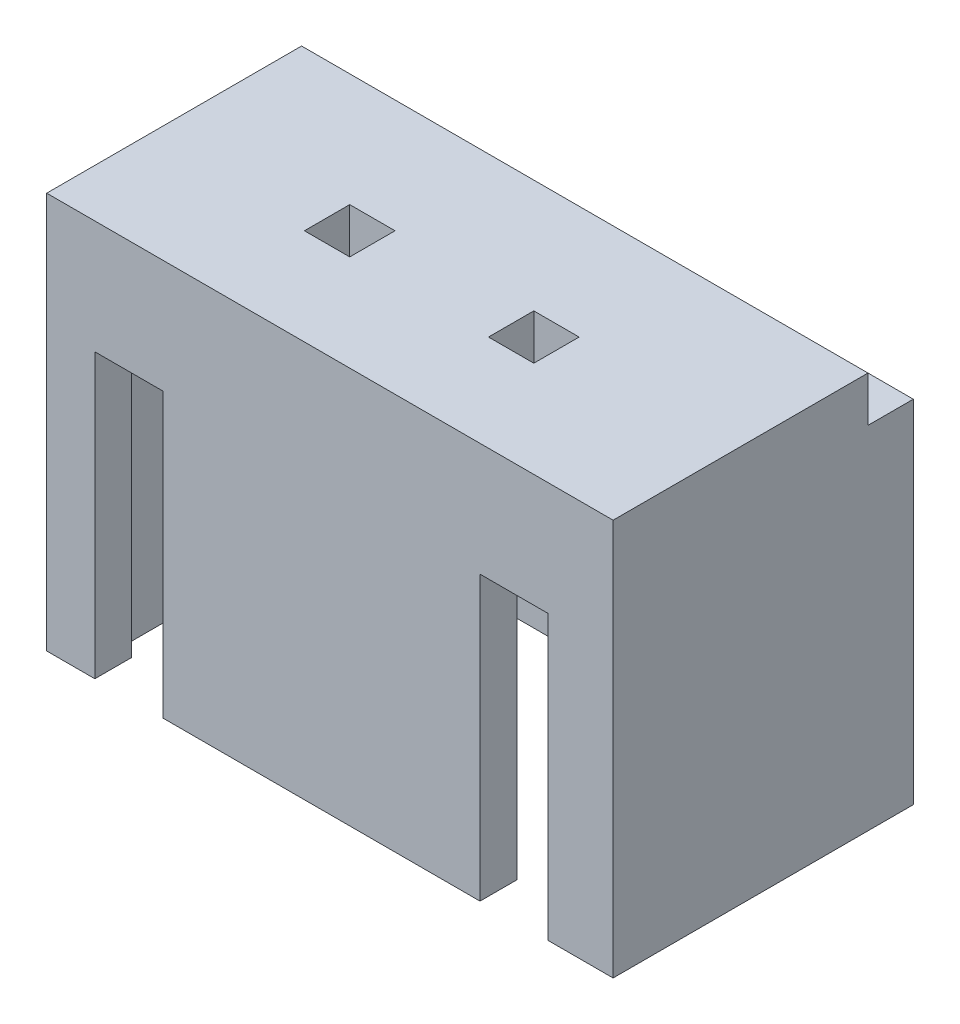
SolidWorks part; units mm, degrees
ref_plane "Front Plane" through (0, 0, 0) normal (0, 0, 1) x (1, 0, 0)
ref_plane "Top Plane" through (0, 0, 0) normal (0, 1, 0) x (1, 0, 0)
ref_plane "Right Plane" through (0, 0, 0) normal (1, 0, 0) x (0, 0, -1)
sketch "Sketch1" plane through (0, 0, 0) normal (0, 1, 0) x (1, 0, 0)
  line L1 (-5, -2.65) -> (5, -2.65)
  line L2 (-5, -2.65) -> (-5, 2.65)
  line L3 (-5, 2.65) -> (5, 2.65)
  line L4 (5, -2.65) -> (5, 2.65)
  line L5 (-5, -2.65) -> (5, 2.65) construction
  line L6 (-5, 2.65) -> (5, -2.65) construction
  point P0 (0, 0)
  dimension "D1" = 10
  dimension "D2" = 5.3
extrude "Boss-Extrude1" add sketch "Sketch1" along normal blind 7
sketch "Sketch3" plane through (0, 0, 0) normal (0, -1, 0) x (1, 0, 0)
  line L1 (-4.4, -2) -> (4.4, -2)
  line L2 (-4.4, -2) -> (-4.4, 2)
  line L3 (-4.4, 2) -> (4.4, 2)
  line L4 (4.4, -2) -> (4.4, 2)
  line L5 (-4.4, -2) -> (4.4, 2) construction
  line L6 (-4.4, 2) -> (4.4, -2) construction
  point P0 (0, 0)
  dimension "D1" = 8.8
  dimension "D2" = 4
extrude "Cut-Extrude1" cut sketch "Sketch3" against normal blind 5
sketch "Sketch4" plane through (0, 0, 2.65) normal (0, 0, 1) x (1, 0, 0)
  line L0 (-5, 0) -> (5, 0) construction
  line L1 (-4.15, 0) -> (-2.95, 0)
  line L2 (-4.15, 0) -> (-4.15, 5)
  line L3 (-4.15, 5) -> (-2.95, 5)
  line L4 (-2.95, 0) -> (-2.95, 5)
  line L6 (2.65, 0) -> (3.85, 0)
  line L7 (2.65, 0) -> (2.65, 5)
  line L8 (2.65, 5) -> (3.85, 5)
  line L9 (3.85, 0) -> (3.85, 5)
  dimension "D1" = 1.2
  dimension "D2" = 1.2
  dimension "D3" = 4.15
  dimension "D4" = 8
  dimension "D5" = 5
extrude "Cut-Extrude2" cut sketch "Sketch4" against normal blind 4
sketch "Sketch5" plane through (0, 7, 0) normal (0, 1, 0) x (1, 0, 0)
  line L0 (5, -2.65) -> (5, 2.65) construction
  line L1 (5, 1.85) -> (-5, 1.85)
  line L2 (5, 1.85) -> (5, 2.65)
  line L3 (5, 2.65) -> (-5, 2.65)
  line L4 (-5, 1.85) -> (-5, 2.65)
  dimension "D1" = 0.8
extrude "Cut-Extrude3" cut sketch "Sketch5" against normal blind 0.8 contours L1 L4 L3 L2
sketch "Sketch6" plane through (0, 7, 0) normal (0, 1, 0) x (1, 0, 0)
  line L2 (1.9, -0.15) -> (1.1, -0.15)
  line L3 (1.9, -0.15) -> (1.9, -0.95)
  line L4 (1.9, -0.95) -> (1.1, -0.95)
  line L5 (1.1, -0.15) -> (1.1, -0.95)
  line L6 (-1.35, -0.95) -> (-2.15, -0.95)
  line L7 (-1.35, -0.95) -> (-1.35, -0.15)
  line L8 (-1.35, -0.15) -> (-2.15, -0.15)
  line L9 (-2.15, -0.95) -> (-2.15, -0.15)
extrude "Cut-Extrude4" cut sketch "Sketch6" against normal blind 10
sketch "Sketch7" plane through (0, 5, 0) normal (0, -1, 0) x (1, 0, 0)
  line L0 (4.4, -2) -> (4.4, 2) construction
  line L1 (-4.4, -2) -> (4.4, -2)
  line L2 (-4.4, -2) -> (-4.4, -1)
  line L3 (-4.4, -1) -> (4.4, -1)
  line L4 (4.4, -2) -> (4.4, -1)
  dimension "D1" = 1
extrude "Cut-Extrude5" cut sketch "Sketch7" against normal blind 0.3
